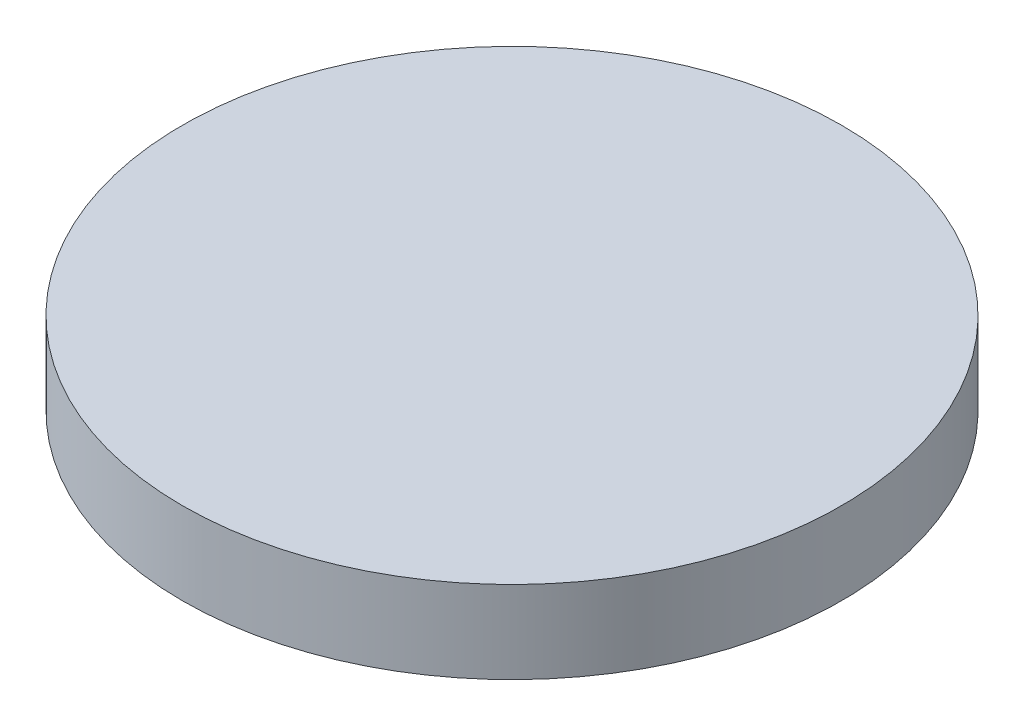
SolidWorks part; units mm, degrees
ref_plane "前视基准面" through (0, 0, 0) normal (0, 0, 1) x (1, 0, 0)
ref_plane "上视基准面" through (0, 0, 0) normal (0, 1, 0) x (1, 0, 0)
ref_plane "右视基准面" through (0, 0, 0) normal (1, 0, 0) x (0, 0, -1)
sketch "草图1" plane through (0, 0, 0) normal (0, 1, 0) x (1, 0, 0)
  circle A0 centre (0, 0) radius 152.4
  dimension "D1" = 304.8
extrude "凸台-拉伸1" add sketch "草图1" along normal blind 38.1
